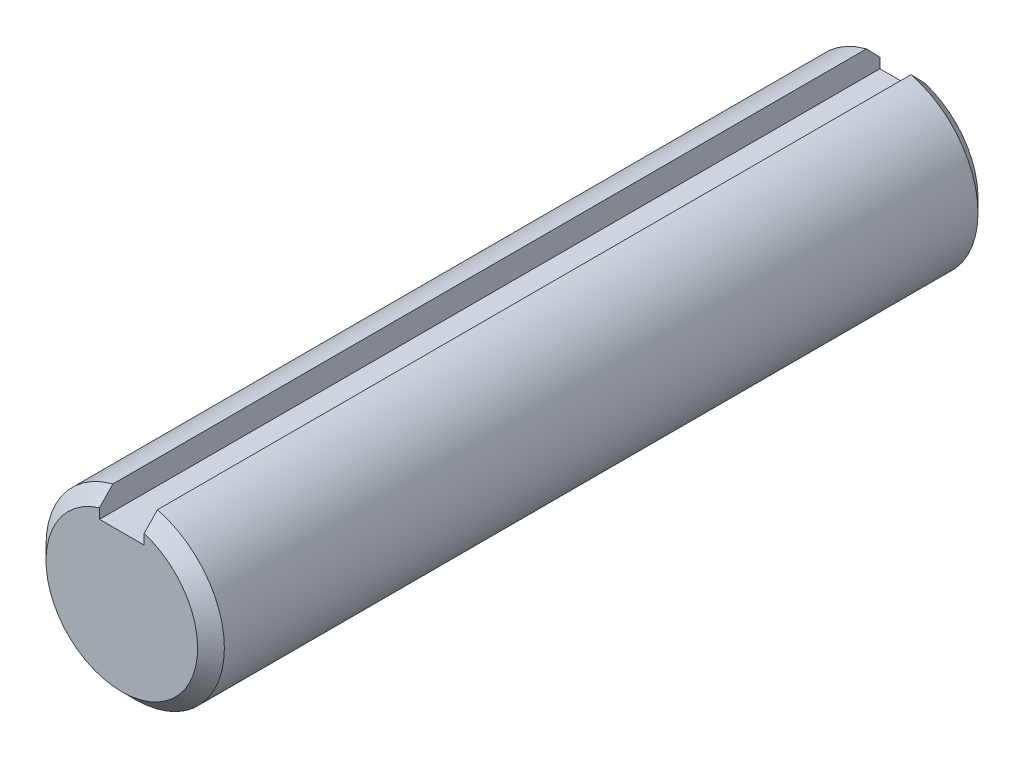
SolidWorks part; units mm, degrees
ref_plane "Front" through (0, 0, 0) normal (0, 0, 1) x (1, 0, 0)
ref_plane "Top" through (0, 0, 0) normal (0, 1, 0) x (1, 0, 0)
ref_plane "Right" through (0, 0, 0) normal (1, 0, 0) x (0, 0, -1)
sketch "Sketch1" plane through (0, 0, 0) normal (0, 0, 1) x (1, 0, 0)
  circle A0 centre (0, 0) radius 4
  dimension "dia" = 8
extrude "Extrude1" add sketch "Sketch1" along normal mid plane 35
sketch "Sketch2" plane through (0, 0, 0) normal (1, 0, 0) x (0, 0, -1)
  point P0 (-17.5, 4)
  point P1 (17.5, 4)
  point P2 (17.5, -4)
chamfer "Chamfer1" distance 0.6 angle 45 2 edges at (4, 0, -17.5) (4, 0, 17.5)
sketch "Sketch3" plane through (0, 0, 0) normal (0, 0, 1) x (1, 0, 0)
  line L1 (-1, 4) -> (1, 4)
  line L2 (-1, 4) -> (-1, 2.8)
  line L3 (-1, 2.8) -> (1, 2.8)
  line L4 (1, 4) -> (1, 2.8)
  dimension "key wd" = 2
  dimension "key dp" = 1.2
extrude "Extrude2" cut sketch "Sketch3" against normal through all and the other way through all
equation "\"D1@Chamfer1\" = \"dia@Sketch1\" * .075"
